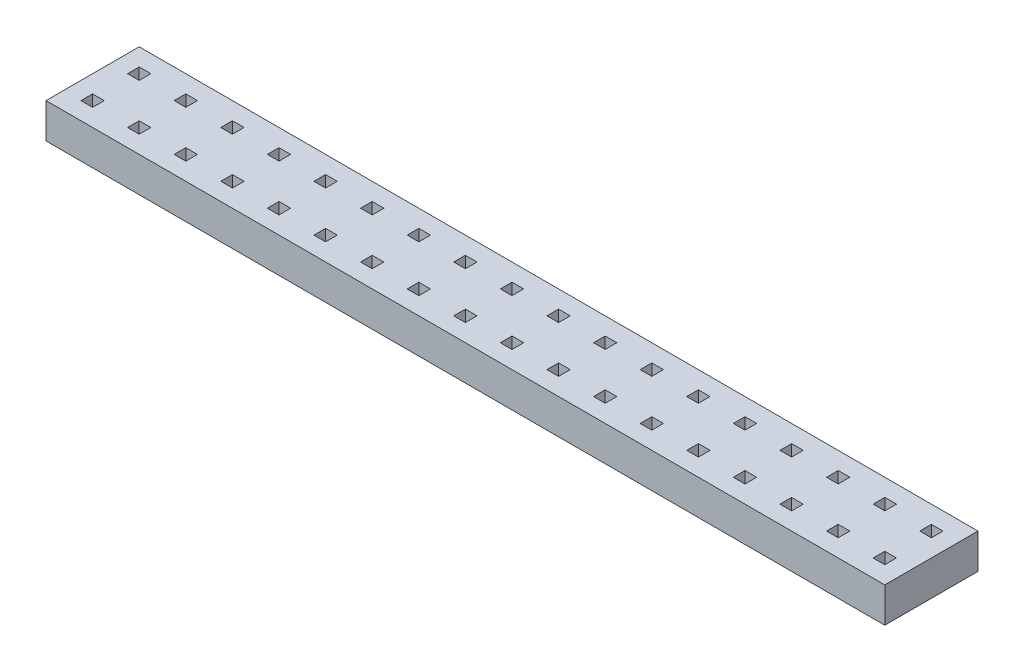
SolidWorks part; units mm, degrees
ref_plane "Front Plane" through (0, 0, 0) normal (0, 0, 1) x (1, 0, 0)
ref_plane "Top Plane" through (0, 0, 0) normal (0, 1, 0) x (1, 0, 0)
ref_plane "Right Plane" through (0, 0, 0) normal (1, 0, 0) x (0, 0, -1)
sketch "Sketch1" plane through (0, 0, 0) normal (0, 1, 0) x (1, 0, 0)
  line L1 (0, 0) -> (36, 0)
  line L2 (0, 0) -> (0, 4)
  line L3 (0, 4) -> (36, 4)
  line L4 (36, 0) -> (36, 4)
extrude "Boss-Extrude1" add sketch "Sketch1" along normal blind 1.5
sketch "Sketch2" plane through (0, 1.5, 0) normal (0, 1, 0) x (1, 0, 0)
  line L0 (2.75, 3.25) -> (2.75, 2.75)
  line L1 (0.75, 3.25) -> (1.25, 3.25)
  line L2 (0.75, 3.25) -> (0.75, 2.75)
  line L3 (0.75, 2.75) -> (1.25, 2.75)
  line L4 (1.25, 3.25) -> (1.25, 2.75)
  line L5 (2.75, 3.25) -> (3.25, 3.25)
  line L6 (3.25, 3.25) -> (3.25, 2.75)
  line L7 (2.75, 2.75) -> (3.25, 2.75)
  line L8 (4.75, 3.25) -> (4.75, 2.75)
  line L9 (4.75, 3.25) -> (5.25, 3.25)
  line L10 (5.25, 3.25) -> (5.25, 2.75)
  line L11 (4.75, 2.75) -> (5.25, 2.75)
  line L12 (6.75, 3.25) -> (6.75, 2.75)
  line L13 (6.75, 3.25) -> (7.25, 3.25)
  line L14 (7.25, 3.25) -> (7.25, 2.75)
  line L15 (6.75, 2.75) -> (7.25, 2.75)
  line L16 (8.75, 3.25) -> (8.75, 2.75)
  line L17 (8.75, 3.25) -> (9.25, 3.25)
  line L18 (9.25, 3.25) -> (9.25, 2.75)
  line L19 (8.75, 2.75) -> (9.25, 2.75)
  line L20 (10.75, 3.25) -> (10.75, 2.75)
  line L21 (10.75, 3.25) -> (11.25, 3.25)
  line L22 (11.25, 3.25) -> (11.25, 2.75)
  line L23 (10.75, 2.75) -> (11.25, 2.75)
  line L24 (12.75, 3.25) -> (12.75, 2.75)
  line L25 (12.75, 3.25) -> (13.25, 3.25)
  line L26 (13.25, 3.25) -> (13.25, 2.75)
  line L27 (12.75, 2.75) -> (13.25, 2.75)
  line L28 (14.75, 3.25) -> (14.75, 2.75)
  line L29 (14.75, 3.25) -> (15.25, 3.25)
  line L30 (15.25, 3.25) -> (15.25, 2.75)
  line L31 (14.75, 2.75) -> (15.25, 2.75)
  line L32 (16.75, 3.25) -> (16.75, 2.75)
  line L33 (16.75, 3.25) -> (17.25, 3.25)
  line L34 (17.25, 3.25) -> (17.25, 2.75)
  line L35 (16.75, 2.75) -> (17.25, 2.75)
  line L36 (18.75, 3.25) -> (18.75, 2.75)
  line L37 (18.75, 3.25) -> (19.25, 3.25)
  line L38 (19.25, 3.25) -> (19.25, 2.75)
  line L39 (18.75, 2.75) -> (19.25, 2.75)
  line L40 (20.75, 3.25) -> (20.75, 2.75)
  line L41 (20.75, 3.25) -> (21.25, 3.25)
  line L42 (21.25, 3.25) -> (21.25, 2.75)
  line L43 (20.75, 2.75) -> (21.25, 2.75)
  line L44 (22.75, 3.25) -> (22.75, 2.75)
  line L45 (22.75, 3.25) -> (23.25, 3.25)
  line L46 (23.25, 3.25) -> (23.25, 2.75)
  line L47 (22.75, 2.75) -> (23.25, 2.75)
  line L48 (24.75, 3.25) -> (24.75, 2.75)
  line L49 (24.75, 3.25) -> (25.25, 3.25)
  line L50 (25.25, 3.25) -> (25.25, 2.75)
  line L51 (24.75, 2.75) -> (25.25, 2.75)
  line L52 (26.75, 3.25) -> (26.75, 2.75)
  line L53 (26.75, 3.25) -> (27.25, 3.25)
  line L54 (27.25, 3.25) -> (27.25, 2.75)
  line L55 (26.75, 2.75) -> (27.25, 2.75)
  line L56 (28.75, 3.25) -> (28.75, 2.75)
  line L57 (28.75, 3.25) -> (29.25, 3.25)
  line L58 (29.25, 3.25) -> (29.25, 2.75)
  line L59 (28.75, 2.75) -> (29.25, 2.75)
  line L60 (30.75, 3.25) -> (30.75, 2.75)
  line L61 (30.75, 3.25) -> (31.25, 3.25)
  line L62 (31.25, 3.25) -> (31.25, 2.75)
  line L63 (30.75, 2.75) -> (31.25, 2.75)
  line L64 (32.75, 3.25) -> (32.75, 2.75)
  line L65 (32.75, 3.25) -> (33.25, 3.25)
  line L66 (33.25, 3.25) -> (33.25, 2.75)
  line L67 (32.75, 2.75) -> (33.25, 2.75)
  line L68 (34.75, 3.25) -> (34.75, 2.75)
  line L69 (34.75, 3.25) -> (35.25, 3.25)
  line L70 (35.25, 3.25) -> (35.25, 2.75)
  line L71 (34.75, 2.75) -> (35.25, 2.75)
  line L72 (0.75, 1.25) -> (0.75, 0.75)
  line L73 (0.75, 1.25) -> (1.25, 1.25)
  line L74 (1.25, 1.25) -> (1.25, 0.75)
  line L75 (0.75, 0.75) -> (1.25, 0.75)
  line L76 (2.75, 1.25) -> (2.75, 0.75)
  line L77 (2.75, 1.25) -> (3.25, 1.25)
  line L78 (3.25, 1.25) -> (3.25, 0.75)
  line L79 (2.75, 0.75) -> (3.25, 0.75)
  line L80 (4.75, 1.25) -> (4.75, 0.75)
  line L81 (4.75, 1.25) -> (5.25, 1.25)
  line L82 (5.25, 1.25) -> (5.25, 0.75)
  line L83 (4.75, 0.75) -> (5.25, 0.75)
  line L84 (6.75, 1.25) -> (6.75, 0.75)
  line L85 (6.75, 1.25) -> (7.25, 1.25)
  line L86 (7.25, 1.25) -> (7.25, 0.75)
  line L87 (6.75, 0.75) -> (7.25, 0.75)
  line L88 (8.75, 1.25) -> (8.75, 0.75)
  line L89 (8.75, 1.25) -> (9.25, 1.25)
  line L90 (9.25, 1.25) -> (9.25, 0.75)
  line L91 (8.75, 0.75) -> (9.25, 0.75)
  line L92 (10.75, 1.25) -> (10.75, 0.75)
  line L93 (10.75, 1.25) -> (11.25, 1.25)
  line L94 (11.25, 1.25) -> (11.25, 0.75)
  line L95 (10.75, 0.75) -> (11.25, 0.75)
  line L96 (12.75, 1.25) -> (12.75, 0.75)
  line L97 (12.75, 1.25) -> (13.25, 1.25)
  line L98 (13.25, 1.25) -> (13.25, 0.75)
  line L99 (12.75, 0.75) -> (13.25, 0.75)
  line L100 (14.75, 1.25) -> (14.75, 0.75)
  line L101 (14.75, 1.25) -> (15.25, 1.25)
  line L102 (15.25, 1.25) -> (15.25, 0.75)
  line L103 (14.75, 0.75) -> (15.25, 0.75)
  line L104 (16.75, 1.25) -> (16.75, 0.75)
  line L105 (16.75, 1.25) -> (17.25, 1.25)
  line L106 (17.25, 1.25) -> (17.25, 0.75)
  line L107 (16.75, 0.75) -> (17.25, 0.75)
  line L108 (18.75, 1.25) -> (18.75, 0.75)
  line L109 (18.75, 1.25) -> (19.25, 1.25)
  line L110 (19.25, 1.25) -> (19.25, 0.75)
  line L111 (18.75, 0.75) -> (19.25, 0.75)
  line L112 (20.75, 1.25) -> (20.75, 0.75)
  line L113 (20.75, 1.25) -> (21.25, 1.25)
  line L114 (21.25, 1.25) -> (21.25, 0.75)
  line L115 (20.75, 0.75) -> (21.25, 0.75)
  line L116 (22.75, 1.25) -> (22.75, 0.75)
  line L117 (22.75, 1.25) -> (23.25, 1.25)
  line L118 (23.25, 1.25) -> (23.25, 0.75)
  line L119 (22.75, 0.75) -> (23.25, 0.75)
  line L120 (24.75, 1.25) -> (24.75, 0.75)
  line L121 (24.75, 1.25) -> (25.25, 1.25)
  line L122 (25.25, 1.25) -> (25.25, 0.75)
  line L123 (24.75, 0.75) -> (25.25, 0.75)
  line L124 (26.75, 1.25) -> (26.75, 0.75)
  line L125 (26.75, 1.25) -> (27.25, 1.25)
  line L126 (27.25, 1.25) -> (27.25, 0.75)
  line L127 (26.75, 0.75) -> (27.25, 0.75)
  line L128 (28.75, 1.25) -> (28.75, 0.75)
  line L129 (28.75, 1.25) -> (29.25, 1.25)
  line L130 (29.25, 1.25) -> (29.25, 0.75)
  line L131 (28.75, 0.75) -> (29.25, 0.75)
  line L132 (30.75, 1.25) -> (30.75, 0.75)
  line L133 (30.75, 1.25) -> (31.25, 1.25)
  line L134 (31.25, 1.25) -> (31.25, 0.75)
  line L135 (30.75, 0.75) -> (31.25, 0.75)
  line L136 (32.75, 1.25) -> (32.75, 0.75)
  line L137 (32.75, 1.25) -> (33.25, 1.25)
  line L138 (33.25, 1.25) -> (33.25, 0.75)
  line L139 (32.75, 0.75) -> (33.25, 0.75)
  line L140 (34.75, 1.25) -> (34.75, 0.75)
  line L141 (34.75, 1.25) -> (35.25, 1.25)
  line L142 (35.25, 1.25) -> (35.25, 0.75)
  line L143 (34.75, 0.75) -> (35.25, 0.75)
  dimension "D1" = 18
  dimension "D2" = 2
extrude "Cut-Extrude1" cut sketch "Sketch2" against normal blind 2
